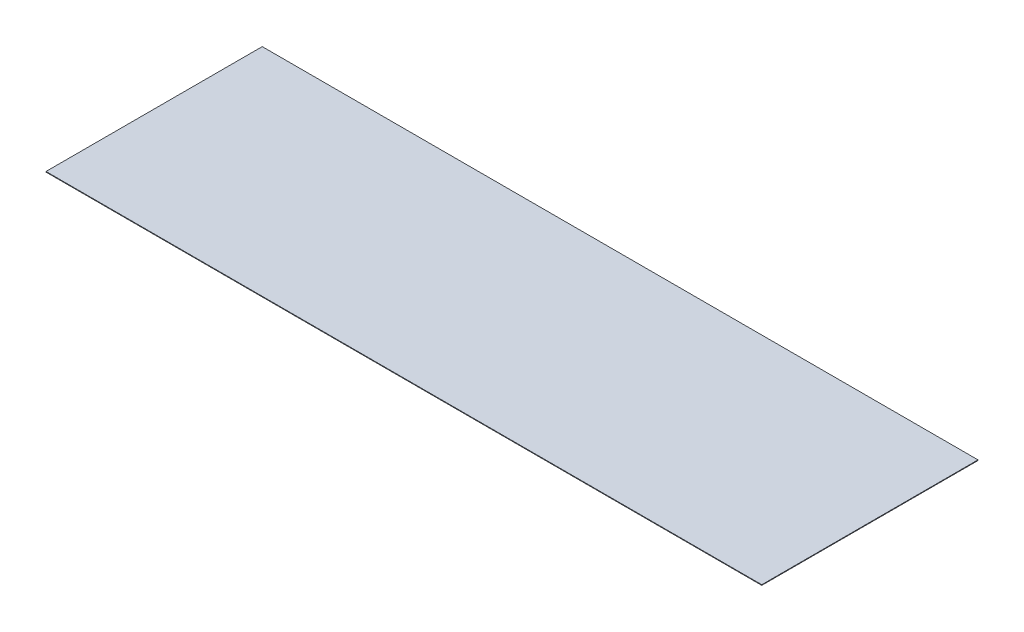
SolidWorks part; units mm, degrees
ref_plane "Front Plane" through (0, 0, 0) normal (0, 0, 1) x (1, 0, 0)
ref_plane "Top Plane" through (0, 0, 0) normal (0, 1, 0) x (1, 0, 0)
ref_plane "Right Plane" through (0, 0, 0) normal (1, 0, 0) x (0, 0, -1)
sketch "Sketch1" plane through (0, 0, 0) normal (0, 1, 0) x (1, 0, 0)
  line L1 (-15240, -4603.75) -> (15240, -4603.75)
  line L2 (-15240, -4603.75) -> (-15240, 4603.75)
  line L3 (-15240, 4603.75) -> (15240, 4603.75)
  line L4 (15240, -4603.75) -> (15240, 4603.75)
  line L5 (-15240, -4603.75) -> (15240, 4603.75) construction
  line L6 (-15240, 4603.75) -> (15240, -4603.75) construction
  point P0 (0, 0)
  dimension "D1" = 30480
  dimension "D2" = 9207.5
extrude "Boss-Extrude1" add sketch "Sketch1" along normal blind 25.4
sketch "Sketch2" plane through (0, 25.4, 0) normal (0, 1, 0) x (1, 0, 0)
  line L0 (-15240, -4603.75) -> (-12192, -4603.75) construction
  line L1 (-15240, -4603.75) -> (15240, -4603.75) construction
  line L2 (-12192, -4603.75) -> (-12192, -4476.75) construction
  line L3 (-15240, 4603.75) -> (-15240, -4603.75) construction
  line L4 (-15240, 0) -> (15240, 0) construction
  line L5 (15240, -4603.75) -> (15240, 4603.75) construction
  line L6 (-9144, -4603.75) -> (-9144, -4476.75) construction
  line L7 (-6096, -4603.75) -> (-6096, -4476.75) construction
  line L8 (-3048, -4603.75) -> (-3048, -4476.75) construction
  line L9 (0, -4603.75) -> (0, -4476.75) construction
  line L10 (3048, -4603.75) -> (3048, -4476.75) construction
  line L11 (6096, -4603.75) -> (6096, -4476.75) construction
  line L12 (9144, -4603.75) -> (9144, -4476.75) construction
  line L13 (12192, -4603.75) -> (12192, -4476.75) construction
  line L14 (12192, 4603.75) -> (12192, 4476.75) construction
  line L15 (9144, 4603.75) -> (9144, 4476.75) construction
  line L16 (6096, 4603.75) -> (6096, 4476.75) construction
  line L17 (3048, 4603.75) -> (3048, 4476.75) construction
  line L18 (0, 4603.75) -> (0, 4476.75) construction
  line L19 (-3048, 4603.75) -> (-3048, 4476.75) construction
  line L20 (-6096, 4603.75) -> (-6096, 4476.75) construction
  line L21 (-9144, 4603.75) -> (-9144, 4476.75) construction
  line L22 (-12192, 4603.75) -> (-12192, 4476.75) construction
  dimension "D1" = 3048
  dimension "D2" = 127
  dimension "D3" = 9
